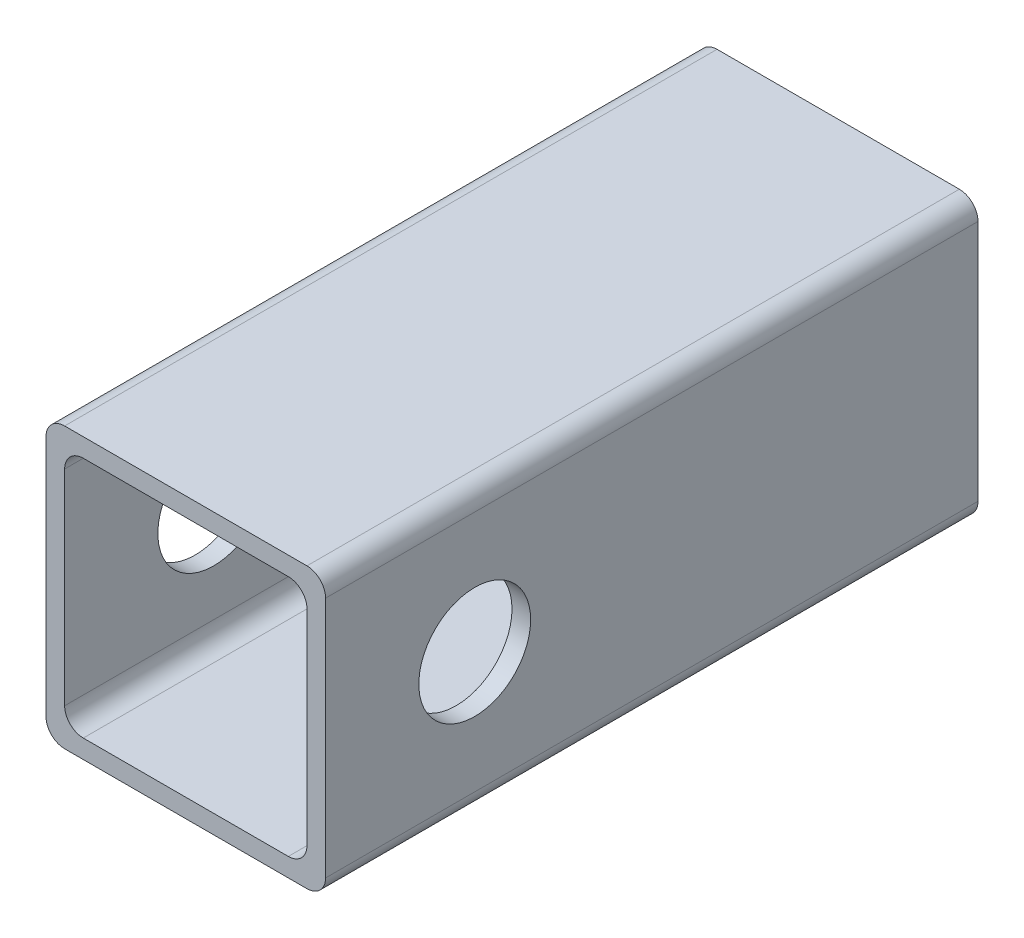
SolidWorks part; units mm, degrees
ref_plane "Płaszczyzna przednia" through (0, 0, 0) normal (0, 0, 1) x (1, 0, 0)
ref_plane "Płaszczyzna górna" through (0, 0, 0) normal (0, 1, 0) x (1, 0, 0)
ref_plane "Płaszczyzna prawa" through (0, 0, 0) normal (1, 0, 0) x (0, 0, -1)
sketch "Szkic1" plane through (0, 0, 0) normal (0, 0, 1) x (1, 0, 0)
  line L0 (4, 28) -> (26, 28)
  line L1 (2, 0) -> (28, 0)
  line L2 (0, 2) -> (0, 28)
  line L3 (2, 30) -> (28, 30)
  line L4 (30, 2) -> (30, 28)
  line L5 (28, 4) -> (28, 26)
  line L6 (4, 2) -> (26, 2)
  line L7 (2, 4) -> (2, 26)
  line L8 (2, 2) -> (28, 2) construction
  line L9 (2, 2) -> (2, 28) construction
  line L10 (0, 0) -> (0, 30) construction
  line L11 (0, 0) -> (30, 0) construction
  line L12 (30, 0) -> (30, 30) construction
  line L13 (28, 2) -> (28, 28) construction
  line L14 (0, 30) -> (30, 30) construction
  line L15 (2, 28) -> (28, 28) construction
  arc A0 (4, 2) -> (2, 4) centre (4, 4) cw
  arc A1 (0, 2) -> (2, 0) centre (2, 2) ccw
  arc A2 (30, 2) -> (28, 0) centre (28, 2) cw
  arc A3 (26, 2) -> (28, 4) centre (26, 4) ccw
  arc A4 (28, 30) -> (30, 28) centre (28, 28) cw
  arc A5 (28, 26) -> (26, 28) centre (26, 26) ccw
  arc A6 (4, 28) -> (2, 26) centre (4, 26) ccw
  arc A7 (2, 30) -> (0, 28) centre (2, 28) ccw
  point P15 (0, 0)
  dimension "D4" = 2
  dimension "D1" = 30
  dimension "D2" = 30
  dimension "D3" = 2
extrude "Dodanie-wyciągnięcie2" add sketch "Szkic1" along normal blind 70
sketch "Szkic2" plane through (30, 0, 0) normal (1, 0, 0) x (0, 0, -1)
  line L0 (0, 2) -> (0, 28) construction
  line L1 (-70, 15) -> (0, 15) construction
  line L2 (-70, 2) -> (-70, 28) construction
  circle A0 centre (-54, 15) radius 6
  dimension "D2" = 12
  dimension "D1" = 54
extrude "Wytnij-wyciągnięcie1" cut sketch "Szkic2" against normal blind 100 contours A0
sketch "Szkic4" [suppressed] plane through (0, 30, 0) normal (0, 1, 0) x (1, 0, 0)
  line L0 (15, 0) -> (15, -250) construction
  line L1 (28, 0) -> (2, 0) construction
  line L2 (28, -250) -> (2, -250) construction
  line L3 (23, -195) -> (23, -55)
  line L4 (7, -195) -> (7, -55)
  arc A0 (7, -195) -> (23, -195) centre (15, -195) ccw
  arc A1 (23, -55) -> (7, -55) centre (15, -55) ccw
  dimension "D3" = 55
  dimension "D1" = 140
  dimension "D2" = 16
extrude "Wytnij-wyciągnięcie3" [suppressed] cut sketch "Szkic4" against normal up to next
sketch "Szkic5" [suppressed] plane through (0, 0, 0) normal (0, 0, -1) x (-1, 0, 0)
  line L0 (-4, 28) -> (0, 28)
  line L1 (0, 28) -> (0, 2)
  line L2 (0, 2) -> (-4, 2)
  line L3 (-4, 2) -> (-4, 28)
  line L4 (0, 28) -> (0, 2) construction
extrude "Wytnij-wyciągnięcie4" [suppressed] cut sketch "Szkic5" against normal up to next
sketch "Szkic6" [suppressed] plane through (0, 30, 0) normal (0, 1, 0) x (1, 0, 0)
  line L0 (15, -47) -> (15, -203) construction
  arc A0 (23, -55) -> (7, -55) centre (15, -55) ccw construction
  arc A1 (7, -195) -> (23, -195) centre (15, -195) ccw construction
